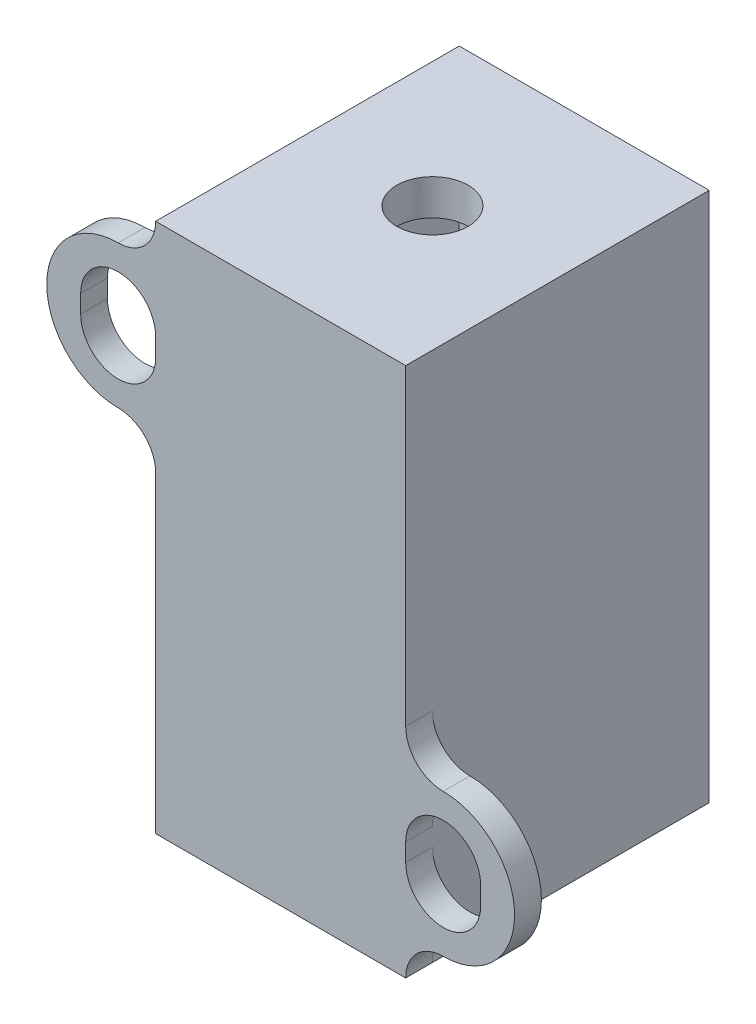
SolidWorks part; units mm, degrees
ref_plane "Front Plane" through (0, 0, 0) normal (0, 0, 1) x (1, 0, 0)
ref_plane "Top Plane" through (0, 0, 0) normal (0, 1, 0) x (1, 0, 0)
ref_plane "Right Plane" through (0, 0, 0) normal (1, 0, 0) x (0, 0, -1)
sketch "Sketch1" plane through (0, 0, 0) normal (0, 0, 1) x (1, 0, 0)
  line L1 (0, 0) -> (14, 0)
  line L2 (0, 0) -> (0, 29.7)
  line L3 (0, 29.7) -> (14, 29.7)
  line L4 (14, 0) -> (14, 29.7)
  dimension "D1" = 29.7
  dimension "D2" = 14
extrude "Boss-Extrude1" add sketch "Sketch1" along normal blind 17
sketch "Sketch2" plane through (0, 29.7, 0) normal (0, 1, 0) x (1, 0, 0)
  line L0 (14, -17) -> (0, 0) construction
  line L1 (0, -17) -> (14, 0) construction
  circle A0 centre (7, -8.5) radius 2
  dimension "D1" = 4
extrude "Cut-Extrude1" cut sketch "Sketch2" against normal through all
sketch "Sketch3" plane through (0, 0, 0) normal (0, -1, 0) x (1, 0, 0)
  circle A0 centre (7, 8.5) radius 4
  dimension "D1" = 8
extrude "Cut-Extrude2" cut sketch "Sketch3" against normal blind 27.7
sketch "Sketch4" plane through (0, 0, 0) normal (0, -1, 0) x (1, 0, 0)
  line L14 (12, 2) -> (12, 15)
  line L15 (12, 15) -> (2, 15)
  line L16 (2, 15) -> (2, 2)
  line L17 (2, 2) -> (12, 2)
  line L18 (12, 2) -> (12, 15)
  line L19 (12, 15) -> (2, 15)
  line L20 (2, 15) -> (2, 2)
  line L21 (2, 2) -> (12, 2)
  dimension "D1" = 2
extrude "Cut-Extrude4" cut sketch "Sketch4" against normal blind 25.7 from offset 2 offset against normal yes
sketch "Sketch5" plane through (0, 0, 17) normal (0, 0, 1) x (1, 0, 0)
  line L0 (7, 29.7) -> (7, 0) construction
  line L1 (-2.1, 23.1) -> (-2.1, 24.1) construction
  line L2 (-4.2, 23.1) -> (-4.2, 24.1)
  line L3 (0, 23.1) -> (0, 24.1)
  line L4 (0, 29.7) -> (0, 0)
  line L5 (0, 0) -> (14, 0)
  line L6 (14, 0) -> (14, 29.7)
  line L7 (14, 29.7) -> (0, 29.7)
  line L9 (0, 0) -> (14, 0)
  line L10 (14, 0) -> (14, 29.7)
  line L11 (14, 29.7) -> (0, 29.7)
  line L12 (0, 14.85) -> (14, 14.85) construction
  line L13 (-4.2, 23.6) -> (0, 23.6) construction
  line L16 (0, 27.6) -> (0, 29.7) construction
  line L19 (0, 27.6) -> (-2.1, 27.6) construction
  line L20 (0, 19.6) -> (-2.1, 19.6) construction
  line L21 (0, 29.7) -> (0, 0) construction
  line L22 (0, 29.7) -> (0, 0)
  line L26 (16.1, 6.6) -> (16.1, 5.6) construction
  line L27 (18.2, 6.6) -> (18.2, 5.6)
  line L28 (14, 6.6) -> (14, 5.6)
  arc A0 (-2.1, 27.6) -> (-2.1, 19.6) centre (-2.1, 23.6) ccw
  arc A1 (-4.2, 23.1) -> (0, 23.1) centre (-2.1, 23.1) ccw
  arc A2 (0, 24.1) -> (-4.2, 24.1) centre (-2.1, 24.1) ccw
  arc A9 (-2.1, 27.6) -> (0, 29.7) centre (-2.1, 29.7) ccw
  arc A10 (-2.1, 19.6) -> (0, 17.5) centre (-2.1, 17.5) cw
  arc A16 (16.1, 10.1) -> (14, 12.2) centre (16.1, 12.2) cw
  arc A17 (18.2, 6.6) -> (14, 6.6) centre (16.1, 6.6) ccw
  arc A18 (14, 5.6) -> (18.2, 5.6) centre (16.1, 5.6) ccw
  arc A19 (16.1, 2.1) -> (16.1, 10.1) centre (16.1, 6.1) ccw
  arc A20 (16.1, 2.1) -> (14, 0) centre (16.1, 0) ccw
  point P9 (-2.1, 23.6)
  point P25 (0, 0)
  point P26 (0, 14.85)
  point P46 (16.1, 6.1)
  line M6 (0, 29.7) -> (0, 0)
  line M8 (14, 0) -> (14, 29.7)
  dimension "D3" = 4
  dimension "D2" = 1
  dimension "D4" = 9.1
  dimension "D1" = 0
extrude "Boss-Extrude2" add sketch "Sketch5" against normal blind 1.5 contours A2 L19 A0 L20 A1 L2 M6 | A20 A19 A16 A17 L27 A18 M8
